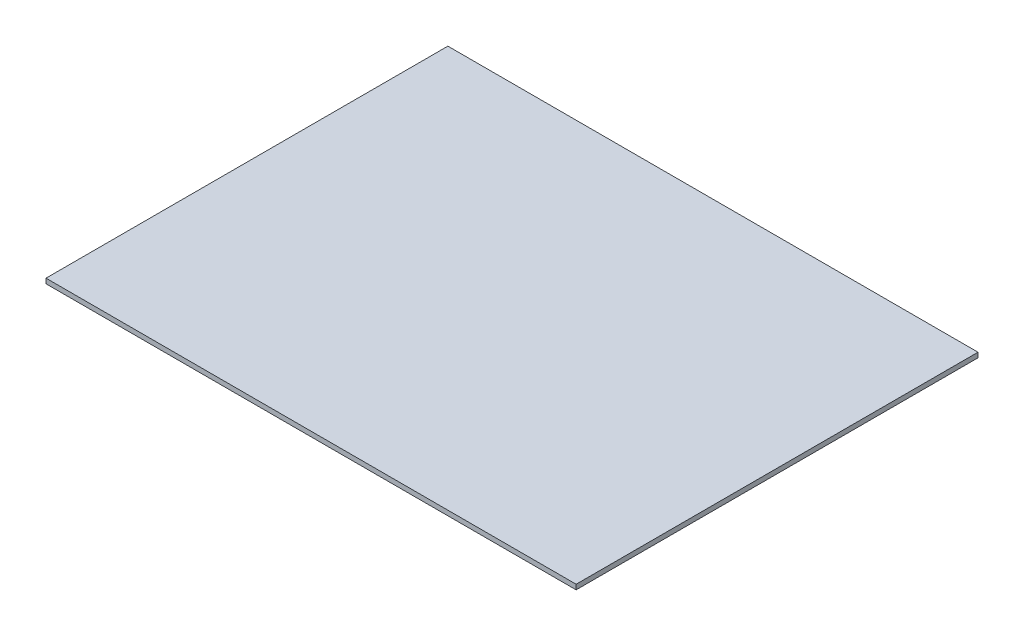
SolidWorks part; units mm, degrees
ref_plane "Спереди" through (0, 0, 0) normal (0, 0, 1) x (1, 0, 0)
ref_plane "Сверху" through (0, 0, 0) normal (0, 1, 0) x (1, 0, 0)
ref_plane "Справа" through (0, 0, 0) normal (1, 0, 0) x (0, 0, -1)
sketch "Эскиз1" plane through (0, 0, 0) normal (0, 1, 0) x (1, 0, 0)
  line L1 (-217, -164.5) -> (217, -164.5)
  line L2 (-217, -164.5) -> (-217, 164.5)
  line L3 (-217, 164.5) -> (217, 164.5)
  line L4 (217, -164.5) -> (217, 164.5)
  line L5 (-217, -164.5) -> (217, 164.5) construction
  line L6 (-217, 164.5) -> (217, -164.5) construction
  point P0 (0, 0)
  dimension "D1" = 329
  dimension "D2" = 434
extrude "Бобышка-Вытянуть1" add sketch "Эскиз1" along normal blind 4
